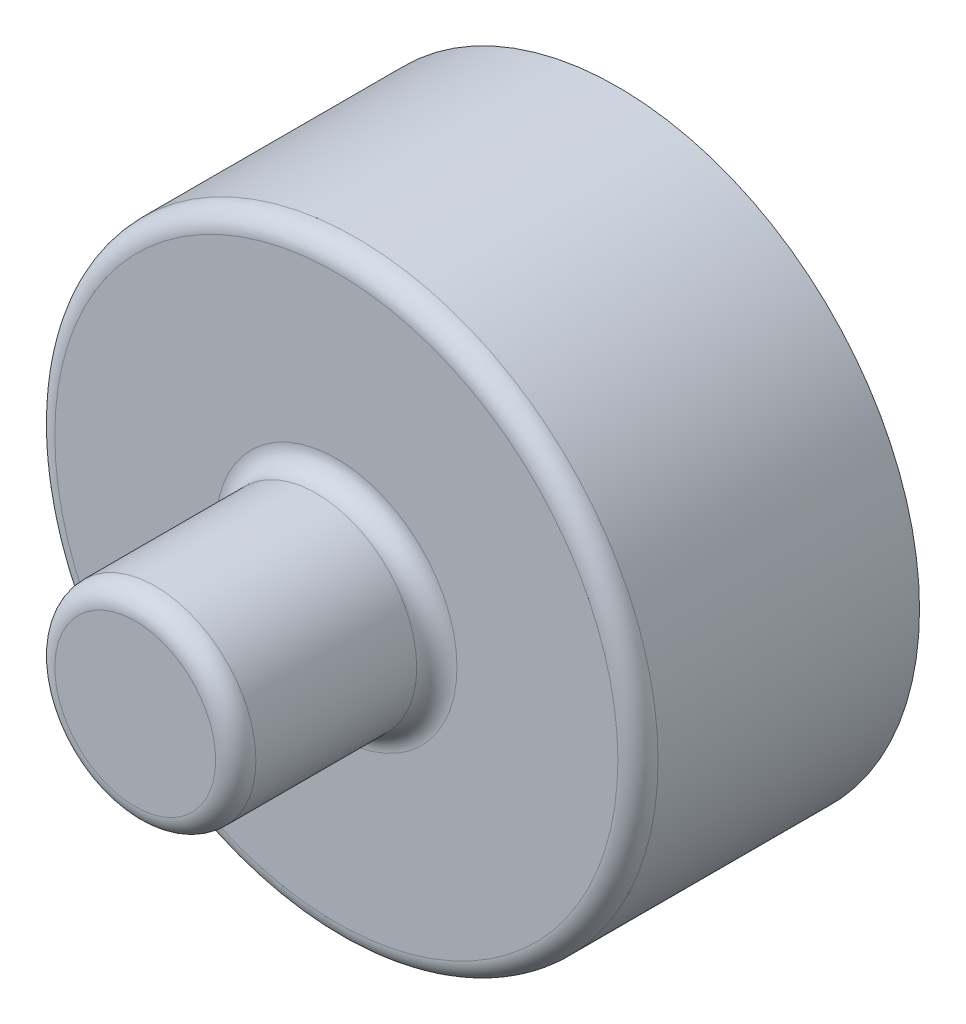
SolidWorks part; units mm, degrees
ref_plane "Plan de face" through (0, 0, 0) normal (0, 0, 1) x (1, 0, 0)
ref_plane "Plan de dessus" through (0, 0, 0) normal (0, 1, 0) x (1, 0, 0)
ref_plane "Plan de droite" through (0, 0, 0) normal (1, 0, 0) x (0, 0, -1)
sketch "Esquisse1" plane through (0, 0, 0) normal (0, 0, 1) x (1, 0, 0)
  circle A0 centre (0, 0) radius 7.5
  dimension "D1" = 15
extrude "Boss.-Extru.1" add sketch "Esquisse1" along normal blind 7
sketch "Esquisse2" plane through (0, 0, 7) normal (0, 0, 1) x (1, 0, 0)
  circle A0 centre (0, 0) radius 2.5
  dimension "D1" = 5
extrude "Boss.-Extru.2" add sketch "Esquisse2" along normal blind 5
fillet "Congé1" radius 0.5 3 edges at (2.5, 0, 7) (7.5, 0, 7) (2.5, 0, 12)
